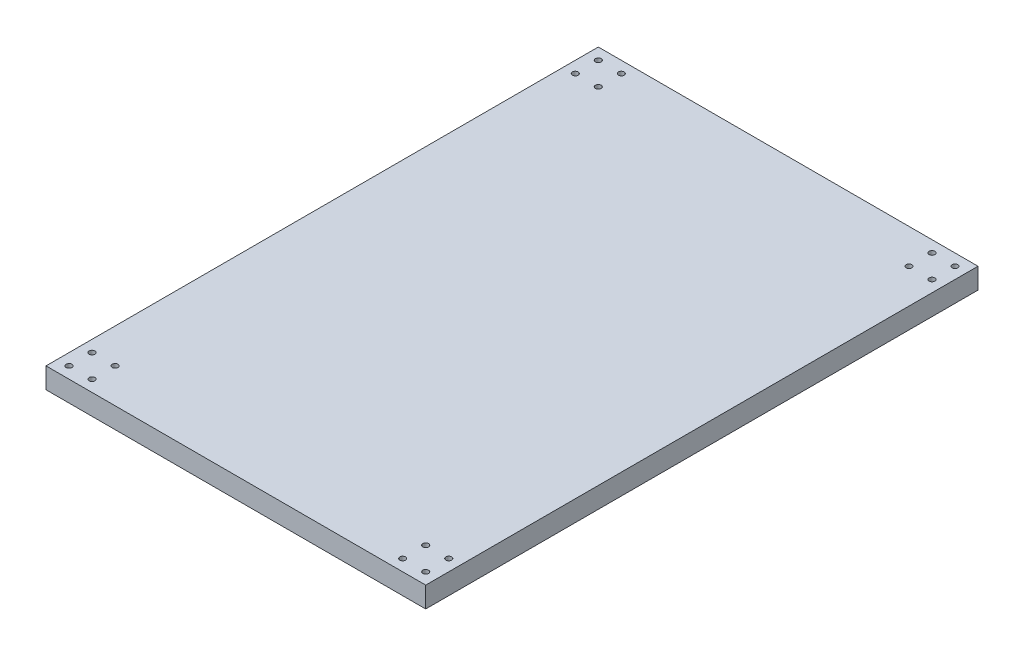
SolidWorks part; units mm, degrees
ref_plane "Front Plane" through (0, 0, 0) normal (0, 0, 1) x (1, 0, 0)
ref_plane "Top Plane" through (0, 0, 0) normal (0, 1, 0) x (1, 0, 0)
ref_plane "Right Plane" through (0, 0, 0) normal (1, 0, 0) x (0, 0, -1)
sketch "Sketch1" plane through (0, 0, 0) normal (0, 1, 0) x (1, 0, 0)
  line L0 (0, 240) -> (330, 240) construction
  line L1 (0, 0) -> (330, 0)
  line L2 (0, 0) -> (0, 480)
  line L3 (0, 480) -> (330, 480)
  line L4 (330, 0) -> (330, 480)
  line L5 (165, 480) -> (165, 0) construction
  circle A0 centre (10, 10) radius 2.5
  circle A1 centre (30, 10) radius 2.5
  circle A2 centre (10, 30) radius 2.5
  circle A3 centre (30, 30) radius 2.5
  circle A4 centre (320, 30) radius 2.5
  circle A5 centre (320, 10) radius 2.5
  circle A6 centre (300, 10) radius 2.5
  circle A7 centre (300, 30) radius 2.5
  circle A8 centre (300, 470) radius 2.5
  circle A9 centre (320, 470) radius 2.5
  circle A10 centre (320, 450) radius 2.5
  circle A11 centre (300, 450) radius 2.5
  circle A12 centre (30, 470) radius 2.5
  circle A13 centre (10, 470) radius 2.5
  circle A14 centre (10, 450) radius 2.5
  circle A15 centre (30, 450) radius 2.5
  dimension "D3" = 5
  dimension "D1" = 330
  dimension "D2" = 480
  dimension "D4" = 20
  dimension "D5" = 20
  dimension "D6" = 20
  dimension "D7" = 10
  dimension "D8" = 10
extrude "Boss-Extrude1" add sketch "Sketch1" along normal blind 18
